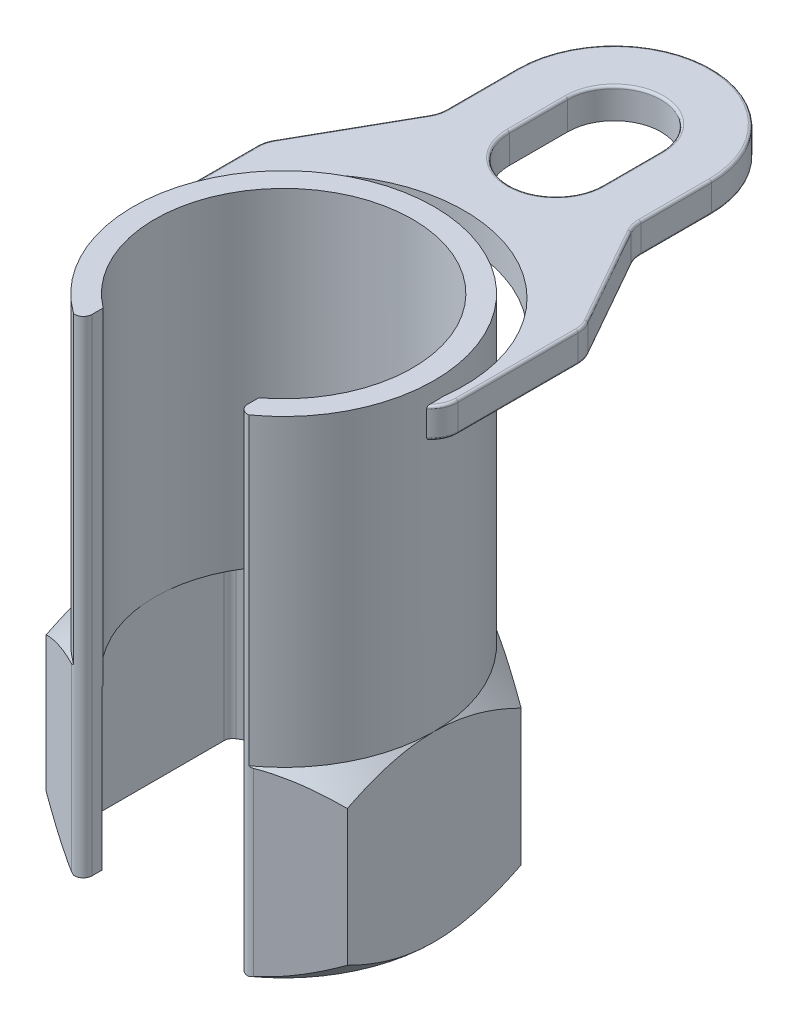
SolidWorks part; units mm, degrees
ref_plane "Front" through (0, 0, 0) normal (0, 0, 1) x (1, 0, 0)
ref_plane "Top" through (0, 0, 0) normal (0, 1, 0) x (1, 0, 0)
ref_plane "Right" through (0, 0, 0) normal (1, 0, 0) x (0, 0, -1)
sketch "Sketch1" plane through (0, 0, 0) normal (0, 1, 0) x (1, 0, 0)
  line L0 (-16, -21.1246) -> (-16, -26.5124)
  line L1 (0, 35.75) -> (-30.9604, 17.875)
  line L2 (0, 11.9615) -> (0, -7.933) construction
  line L3 (-30.9604, 17.875) -> (-30.9604, -17.875)
  line L4 (-30.9604, -17.875) -> (-16, -26.5124)
  line L5 (16, -26.5124) -> (30.9604, -17.875)
  line L6 (30.9604, -17.875) -> (30.9604, 17.875)
  line L7 (30.9604, 17.875) -> (0, 35.75)
  line L8 (16, -21.1246) -> (16, -26.5124)
  arc A0 (16, -26.5056) -> (-16, -26.5056) centre (0, 0) ccw construction
  arc A1 (16, -21.1246) -> (-16, -21.1246) centre (0, 0) ccw
  point P18 (-30.9604, -17.875)
  point P26 (30.9604, 17.875)
  dimension "D" = 71.5
  dimension "D2" = 53
  dimension "C" = 32
extrude "Extrude1" add sketch "Sketch1" along normal blind 37.5
sketch "Sketch3" plane through (0, 37.5, 0) normal (0, 1, 0) x (-1, 0, 0)
  line L0 (-30.9604, 17.875) -> (-30.9604, -17.875) construction
  line L2 (-16, 26.5055) -> (-16, 21.1246)
  line L3 (16, 26.5055) -> (16, 21.1246)
  arc A0 (-16, 21.1246) -> (16, 21.1246) centre (0, 0) ccw
  arc A1 (-16, 21.1246) -> (16, 21.1246) centre (0, 0) ccw construction
  arc A2 (-16, 26.5055) -> (16, 26.5055) centre (0, 0) ccw
  dimension "D1" = 0.0001
extrude "Extrude2" add sketch "Sketch3" along normal blind 62.5
sketch "Sketch8" plane through (0, 0, 0) normal (0, -1, 0) x (1, 0, 0)
  line L1 (30.9604, 17.875) -> (30.9604, -17.875) construction
  circle A0 centre (0, 0) radius 30.9604
extrude "Cut-Extrude4" cut sketch "Sketch8" against normal through all draft 45 flip side to cut
sketch "Sketch19" plane through (0, 37.5, 0) normal (0, 1, 0) x (-1, 0, 0)
  circle A1 centre (0, 0) radius 30.9603
  arc A2 (-16, 26.5055) -> (16, 26.5055) centre (0, 0) ccw construction
extrude "Cut-Extrude6" cut sketch "Sketch19" against normal through all draft 45 flip side to cut
sketch "Sketch26" plane through (0, 0, 0) normal (0, -1, 0) x (1, 0, 0)
  line L1 (-26.5, -15.2998) -> (0, -30.5996)
  line L2 (0, -30.5996) -> (26.5, -15.2998)
  line L3 (26.5, -15.2998) -> (26.5, 15.2998)
  line L4 (26.5, 15.2998) -> (0, 30.5996)
  line L5 (0, 30.5996) -> (-26.5, 15.2998)
  line L6 (-26.5, 15.2998) -> (-26.5, -15.2998)
  circle A0 centre (0, 0) radius 26.5 construction
  dimension "D1" = 53
extrude "Cut-Extrude9" cut sketch "Sketch26" against normal up to vertex (38.5 mm away)
fillet "Fillet1" radius 1.8 7 edges at (-26.5, 16.3552, -15.2998) (-26.5, 16.3552, 15.2998) (26.5, 16.3552, 15.2998) (26.5, 16.3552, -15.2998) (-16, 18.75, 26.5124) (16, 18.7499, 26.5124) (0, 16.3552, -30.5996)
sketch "Sketch4" [suppressed] plane through (0, 0, 0) normal (0, 1, 0) x (-1, 0, 0)
  line L0 (0, -11.2014) -> (0, 12.8888) construction
  line L1 (-10, -2.5) -> (10, -2.5)
  line L2 (-10, -2.5) -> (-10, 3.8)
  line L3 (-10, 3.8) -> (10, 3.8)
  line L4 (10, -2.5) -> (10, 3.8)
  line L5 (16.2585, 0) -> (-21.4153, 0) construction
  dimension "D1" = 53
  dimension "D2" = 9.5
  dimension "D3" = 8.2
sketch "Sketch12" [suppressed] plane through (0, 0, 0) normal (0, 1, 0) x (1, 0, 0)
  line L0 (-11, -4) -> (11, -4)
  line L1 (0, 0) -> (-11.4274, 0) construction
  line L2 (-11, 2.7) -> (11, 2.7)
  line L3 (-4.5, 14.3091) -> (4.5, 14.3091)
  line L4 (-7, 3.2909) -> (-7, -3.2909) construction
  line L5 (7, -3.2909) -> (7, 3.2909) construction
  arc A0 (-11, -4) -> (11, -4) centre (0, 0) ccw
  arc A1 (-6.3246, -3) -> (6.3246, -3) centre (0, 0) ccw construction
  arc A2 (-4.5, 14.3091) -> (-11, 2.7) centre (2.617, 2.7) ccw
  arc A3 (-4.5, 14.3091) -> (4.5, 14.3091) centre (0, 0) ccw construction
  arc A4 (4.5, 14.3091) -> (11, 2.7) centre (-2.617, 2.7) cw
ref_plane "Plane3" through (0, 90, 0) normal (0, 1, 0) x (-1, 0, 0)
sketch "Sketch16" plane through (0, 90, 0) normal (0, 1, 0) x (-1, 0, 0)
  line L5 (0, 0) -> (0, 54.2988) construction
  line L6 (-20, -68) -> (-20, -53.4731)
  line L10 (20, -53.4731) -> (20, -68)
  line L11 (32.2752, -30.2824) -> (20.7248, -50.7176)
  line L12 (-32.2752, -30.2824) -> (-20.7248, -50.7176)
  line L13 (-33, -2.8522) -> (-33, -27.5269)
  line L14 (33, -2.8522) -> (33, -27.5269)
  line L15 (38.3763, 1.5) -> (-38.1367, 1.5) construction
  arc A0 (-18.0109, 25.1823) -> (18.0109, 25.1823) centre (0, 0) ccw construction
  arc A1 (-30.9239, 1.5) -> (30.9239, 1.5) centre (0, 0) ccw
  arc A2 (33, -2.8522) -> (30.9239, 1.5) centre (27.4, -2.8522) ccw
  arc A3 (-33, -2.8522) -> (-30.9239, 1.5) centre (-27.4, -2.8522) cw
  arc A4 (-33, -27.5269) -> (-32.2752, -30.2824) centre (-27.4, -27.5269) ccw
  arc A5 (-20.7248, -50.7176) -> (-20, -53.4731) centre (-25.6, -53.4731) cw
  arc A7 (33, -27.5269) -> (32.2752, -30.2824) centre (27.4, -27.5269) cw
  arc A8 (20.7248, -50.7176) -> (20, -53.4731) centre (25.6, -53.4731) ccw
  arc A15 (20, -68) -> (-20, -68) centre (0, -68) cw
  point P18 (-33, -29)
  point P22 (-20, -52)
  point P25 (33, -29)
  point P30 (20, -52)
  dimension "D1" = 66
  dimension "D2" = 29
  dimension "D3" = 52
  dimension "D4" = 5.6
  dimension "D6" = 40
  dimension "D7" = 68
  dimension "D14" = 1.5
extrude "Extrude7" add sketch "Sketch16" along normal blind 6.2
sketch "Sketch25" plane through (0, 96.2, 0) normal (0, -1, 0) x (1, 0, 0)
  line L1 (-29.4486, 0) -> (37.9585, 0) construction
  line L3 (0, -57.3769) -> (0, 10.8445) construction
  line L4 (-9.6, -68) -> (-9.6, -56)
  line L5 (9.6, -68) -> (9.6, -56)
  arc A0 (-18.0109, 25.1823) -> (18.0109, 25.1823) centre (0, 0) ccw construction
  arc A2 (-20, -68) -> (20, -68) centre (0, -68) ccw construction
  arc A6 (30.8956, -2) -> (-30.8956, -2) centre (0, 0) cw
  arc A7 (30.8956, -2) -> (-30.8956, -2) centre (0, -6) cw
  arc A8 (9.6, -68) -> (-9.6, -68) centre (0, -68) cw
  arc A9 (9.6, -56) -> (-9.6, -56) centre (0, -56) ccw
  dimension "D1" = 32
  dimension "D2" = 19.2
  dimension "D3" = 2
  dimension "D4" = 6
extrude "Cut-Extrude8" cut sketch "Sketch25" along normal up to next
fillet "Fillet4" radius 0.5 30 edges at (9.6, 96.2, -62) (0, 96.2, -77.6) (-9.6, 96.2, -62) (32.4544, 96.2, -0.4412) (33, 96.2, -15.1896) (32.8158, 96.2, -28.9515) (-32.4544, 96.2, -0.4412) (-33, 96.2, -15.1896) (-32.8158, 96.2, -28.9515) (-26.5, 96.2, -40.5) (-20.1842, 96.2, -52.0485) (-20, 96.2, -60.7365) (0, 96.2, -88) (20, 96.2, -60.7365) (20.1842, 96.2, -52.0485) (32.4544, 90, -0.4412) (33, 90, -15.1896) (32.8158, 90, -28.9515) (-32.4544, 90, -0.4412) (-33, 90, -15.1896) (-32.8158, 90, -28.9515) (-26.5, 90, -40.5) (-20.1842, 90, -52.0485) (-20, 90, -60.7365) (0, 90, -88) (20, 90, -60.7365) (20.1842, 90, -52.0485) (0, 96.2, -46.4) (26.5, 96.2, -40.5) (26.5, 90, -40.5)
sketch "Sketch20" [suppressed] plane through (0, 0, 0) normal (0, 1, 0) x (1, 0, 0)
  line L0 (0, 0) -> (0, 12.8849) construction
  line L1 (-7.5, -9.3675) -> (-7.5, -14.4157)
  line L2 (7.5, -9.3675) -> (7.5, -14.4157)
  arc A0 (7.5, -14.4157) -> (-7.5, -14.4157) centre (0, 0) ccw
  arc A1 (7.5, -9.3675) -> (-7.5, -9.3675) centre (0, 0) ccw
  circle A2 centre (0, 0) radius 16.25 construction
  circle A3 centre (0, 0) radius 12 construction
  dimension "D1" = 71.5
  dimension "D2" = 53
  dimension "D3" = 32
extrude "Extrude3" [suppressed] add sketch "Sketch20" along normal blind 62
ref_plane "Plane7" [suppressed] through (0, 41.999, 0) normal (0, 1, 0) x (-1, 0, 0)
sketch "Sketch21" [suppressed] plane through (0, 41.999, 0) normal (0, 1, 0) x (-1, 0, 0)
  line L1 (2.5, 16.0565) -> (2.5, 19.8734)
  line L2 (7.5, 14.4157) -> (7.5, 9.3675) construction
  line L4 (7.5, 14.4157) -> (7.5, 18.5729)
  arc A1 (2.5, 16.0565) -> (7.5, 14.4157) centre (0, 0) ccw
  arc A2 (2.5, 19.8734) -> (7.5, 18.5729) centre (0, 0) ccw
  arc A3 (-7.5, 14.4157) -> (7.5, 14.4157) centre (0, 0) ccw construction
  dimension "D1" = 5.58
  dimension "D2" = 2.5
extrude "Extrude4" [suppressed] add sketch "Sketch21" against normal blind 18 separate body
ref_plane "Plane6" [suppressed] through (5.0421, 41.999, -19.385) normal (0.2517, 0, -0.9678) x (-0.9678, 0, -0.2517)
sketch "Sketch22" [suppressed] plane through (5.0421, 41.999, -19.385) normal (0.2517, 0, -0.9678) x (-0.9678, 0, -0.2517)
  line L0 (20.03, 0) -> (-20.03, 0) construction
  line L1 (0, 0) -> (0, 14.8678) construction
  line L2 (-3.2, -3.3) -> (3.2, -3.3)
  line L3 (-3.2, -3.3) -> (-3.2, -9.7)
  line L4 (-3.2, -9.7) -> (3.2, -9.7)
  line L5 (3.2, -3.3) -> (3.2, -9.7)
  line L7 (-18.9345, -6.5) -> (19.4735, -6.5) construction
  dimension "D1" = 10.4
  dimension "D2" = 9
  dimension "D3" = 10.4
extrude "Extrude5" [suppressed] add sketch "Sketch22" along normal blind 22 and the other way up to next
sketch "Sketch23" [suppressed] plane through (8.0628, 0, -30.9986) normal (0.2517, 0, -0.9678) x (-0.9678, 0, -0.2517)
  circle A0 centre (0, 35.499) radius 4.5255
extrude "Extrude6" [suppressed] add sketch "Sketch23" along normal blind 52 draft 2
dome "Dome1" [suppressed] faces to dome 1 distance 3 parameters "D1"=3
sketch "Sketch24" [suppressed] plane through (0, 0, 0) normal (0, -1, 0) x (1, 0, 0)
  line L2 (-12, 6.9282) -> (-12, -6.9282)
  line L3 (-12, -6.9282) -> (0, -13.8564)
  line L4 (0, -13.8564) -> (12, -6.9282)
  line L5 (12, -6.9282) -> (12, 6.9282)
  line L6 (12, 6.9282) -> (0, 13.8564)
  line L7 (0, 13.8564) -> (-12, 6.9282)
  circle A0 centre (0, 0) radius 12 construction
  dimension "D1" = 53
extrude "Cut-Extrude7" [suppressed] cut sketch "Sketch24" against normal through all
fillet "Fillet2" [suppressed] radius 0.5
fillet "Fillet3" [suppressed] radius 0.5
fillet "Fillet5" [suppressed] radius 1
